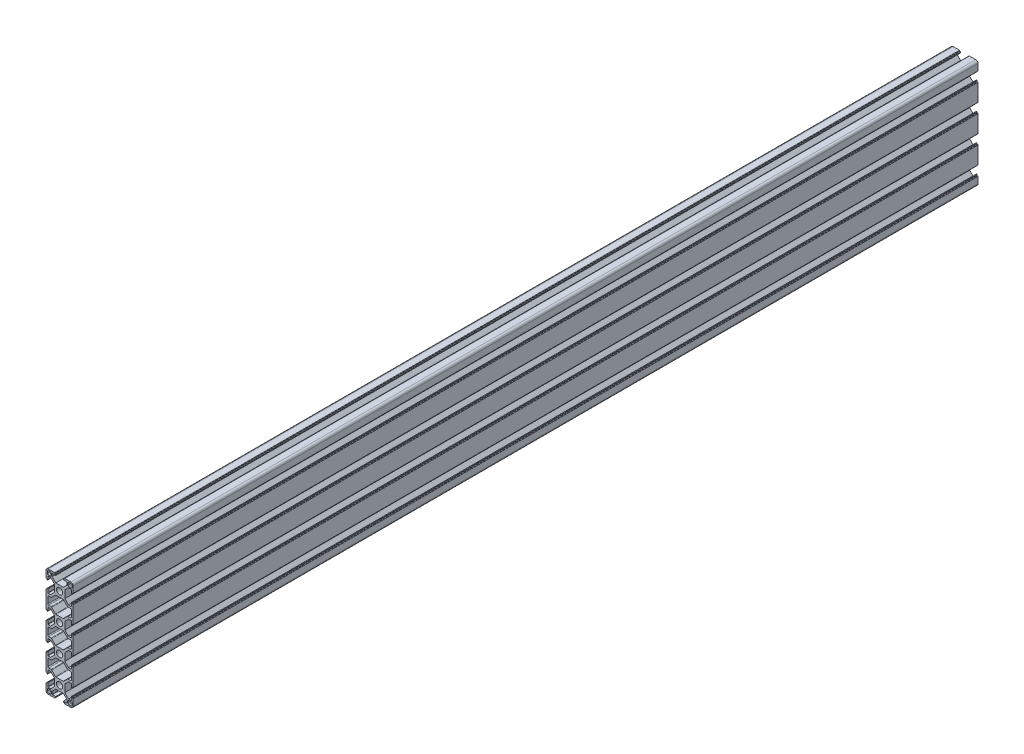
SolidWorks part; units mm, degrees
material "6063 T5"
ref_plane "Спереди" through (0, 0, 0) normal (0, 0, 1) x (1, 0, 0)
ref_plane "Сверху" through (0, 0, 0) normal (0, 1, 0) x (1, 0, 0)
ref_plane "Справа" through (0, 0, 0) normal (1, 0, 0) x (0, 0, -1)
sketch "Эскиз1" plane through (0, 0, 0) normal (0, 0, 1) x (1, 0, 0)
  line L0 (42.4804, 14.8887) -> (42.4804, -45.1113) construction
  line L1 (-15, 8.25) -> (-15, 12.5)
  line L2 (-12.5, 15) -> (-8.25, 15)
  line L3 (8.25, 15) -> (12.5, 15)
  line L4 (15, 12.5) -> (15, 8.25)
  line L5 (12.55, 9.35) -> (10.35, 9.35)
  line L6 (-12.55, 13.55) -> (-10.35, 13.55)
  line L7 (-13.55, 12.55) -> (-13.55, 10.35)
  line L8 (-12.55, 9.35) -> (-10.35, 9.35)
  line L9 (-9.35, 12.55) -> (-9.35, 10.35)
  line L10 (13.55, 12.55) -> (13.55, 10.35)
  line L11 (12.55, 13.55) -> (10.35, 13.55)
  line L12 (9.35, 12.55) -> (9.35, 10.35)
  line L13 (0, 0) -> (0, -30) construction
  line L14 (0, -15) -> (-22.4838, -15) construction
  line L23 (0, -30) -> (0, -60) construction
  line L24 (0, -45) -> (-22.4838, -45) construction
  line L25 (0, -75) -> (-22.4838, -75) construction
  line L26 (0, -90) -> (0, -60) construction
  line L27 (-15, -8.25) -> (-15, -21.75)
  line L28 (15, -8.25) -> (15, -21.75)
  line L29 (-13, -18.5) -> (-13, -11.5)
  line L30 (-12, -10.5) -> (-9.4029, -10.5)
  line L31 (-8.6958, -10.2071) -> (-4.5816, -6.0929)
  line L32 (-3.8745, -5.8) -> (3.8745, -5.8)
  line L33 (8.6958, -10.2071) -> (4.5816, -6.0929)
  line L34 (12, -10.5) -> (9.4029, -10.5)
  line L35 (13, -18.5) -> (13, -11.5)
  line L36 (12, -19.5) -> (9.4029, -19.5)
  line L37 (8.6958, -19.7929) -> (4.5816, -23.9071)
  line L38 (-3.8745, -24.2) -> (3.8745, -24.2)
  line L39 (-8.6958, -19.7929) -> (-4.5816, -23.9071)
  line L40 (-12, -19.5) -> (-9.4029, -19.5)
  line L41 (-12, -70.5) -> (-9.4029, -70.5)
  line L42 (-8.6958, -70.2071) -> (-4.5816, -66.0929)
  line L43 (-3.8745, -65.8) -> (3.8745, -65.8)
  line L44 (8.6958, -70.2071) -> (4.5816, -66.0929)
  line L45 (12, -70.5) -> (9.4029, -70.5)
  line L46 (13, -71.5) -> (13, -78.5)
  line L47 (12, -79.5) -> (9.4029, -79.5)
  line L48 (8.6958, -79.7929) -> (4.5816, -83.9071)
  line L49 (-3.8745, -84.2) -> (3.8745, -84.2)
  line L50 (-8.6958, -79.7929) -> (-4.5816, -83.9071)
  line L51 (-12, -79.5) -> (-9.4029, -79.5)
  line L52 (-13, -71.5) -> (-13, -78.5)
  line L53 (15, -81.75) -> (15, -68.25)
  line L54 (-15, -81.75) -> (-15, -68.25)
  line L55 (9.35, -102.55) -> (9.35, -100.35)
  line L56 (12.55, -103.55) -> (10.35, -103.55)
  line L57 (13.55, -102.55) -> (13.55, -100.35)
  line L58 (-9.35, -102.55) -> (-9.35, -100.35)
  line L59 (-12.55, -99.35) -> (-10.35, -99.35)
  line L60 (-13.55, -102.55) -> (-13.55, -100.35)
  line L61 (-12.55, -103.55) -> (-10.35, -103.55)
  line L62 (12.55, -99.35) -> (10.35, -99.35)
  line L63 (15, -102.5) -> (15, -98.25)
  line L64 (8.25, -105) -> (12.5, -105)
  line L65 (-12.5, -105) -> (-8.25, -105)
  line L66 (-15, -98.25) -> (-15, -102.5)
  line L67 (-15, -38.25) -> (-15, -51.75)
  line L68 (15, -38.25) -> (15, -51.75)
  line L69 (12, -40.5) -> (9.4029, -40.5)
  line L70 (13, -41.5) -> (13, -48.5)
  line L71 (12, -49.5) -> (9.4029, -49.5)
  line L72 (8.6958, -49.7929) -> (4.5816, -53.9071)
  line L73 (-3.8745, -54.2) -> (3.8745, -54.2)
  line L74 (-8.6958, -49.7929) -> (-4.5816, -53.9071)
  line L75 (-12, -49.5) -> (-9.4029, -49.5)
  line L76 (-13, -41.5) -> (-13, -48.5)
  line L77 (-12, -40.5) -> (-9.4029, -40.5)
  line L78 (-8.6958, -40.2071) -> (-4.5816, -36.0929)
  line L79 (-3.8745, -35.8) -> (3.8745, -35.8)
  line L80 (8.6958, -40.2071) -> (4.5816, -36.0929)
  line L81 (-21.0907, 14.8856) -> (-21.0907, -105.1144) construction
  arc A0 (12.5, 15) -> (15, 12.5) centre (12.5, 12.5) cw
  arc A1 (-15, 12.5) -> (-12.5, 15) centre (-12.5, 12.5) cw
  arc A2 (-13.55, 10.35) -> (-12.55, 9.35) centre (-12.55, 10.35) ccw
  arc A3 (-10.35, 9.35) -> (-9.35, 10.35) centre (-10.35, 10.35) ccw
  arc A4 (-10.35, 13.55) -> (-9.35, 12.55) centre (-10.35, 12.55) cw
  arc A5 (-12.55, 13.55) -> (-13.55, 12.55) centre (-12.55, 12.55) ccw
  arc A6 (10.35, 9.35) -> (9.35, 10.35) centre (10.35, 10.35) cw
  arc A7 (13.55, 10.35) -> (12.55, 9.35) centre (12.55, 10.35) cw
  arc A8 (12.55, 13.55) -> (13.55, 12.55) centre (12.55, 12.55) cw
  arc A9 (10.35, 13.55) -> (9.35, 12.55) centre (10.35, 12.55) ccw
  circle A10 centre (0, 0) radius 3.4
  circle A11 centre (0, -30) radius 3.4
  arc A20 (-13, -71.5) -> (-12, -70.5) centre (-12, -71.5) cw
  arc A21 (-9.4029, -70.5) -> (-8.6958, -70.2071) centre (-9.4029, -69.5) ccw
  arc A22 (-4.5816, -6.0929) -> (-3.8745, -5.8) centre (-3.8745, -6.8) cw
  arc A23 (-9.4029, -10.5) -> (-8.6958, -10.2071) centre (-9.4029, -9.5) ccw
  arc A24 (-13, -11.5) -> (-12, -10.5) centre (-12, -11.5) cw
  arc A25 (4.5816, -6.0929) -> (3.8745, -5.8) centre (3.8745, -6.8) ccw
  arc A26 (9.4029, -10.5) -> (8.6958, -10.2071) centre (9.4029, -9.5) cw
  arc A27 (13, -11.5) -> (12, -10.5) centre (12, -11.5) ccw
  arc A28 (13, -18.5) -> (12, -19.5) centre (12, -18.5) cw
  arc A29 (9.4029, -19.5) -> (8.6958, -19.7929) centre (9.4029, -20.5) ccw
  arc A30 (4.5816, -23.9071) -> (3.8745, -24.2) centre (3.8745, -23.2) cw
  arc A31 (-4.5816, -23.9071) -> (-3.8745, -24.2) centre (-3.8745, -23.2) ccw
  arc A32 (-9.4029, -19.5) -> (-8.6958, -19.7929) centre (-9.4029, -20.5) cw
  arc A33 (-13, -18.5) -> (-12, -19.5) centre (-12, -18.5) ccw
  arc A34 (-4.5816, -66.0929) -> (-3.8745, -65.8) centre (-3.8745, -66.8) cw
  arc A35 (4.5816, -66.0929) -> (3.8745, -65.8) centre (3.8745, -66.8) ccw
  arc A36 (9.4029, -70.5) -> (8.6958, -70.2071) centre (9.4029, -69.5) cw
  arc A37 (13, -71.5) -> (12, -70.5) centre (12, -71.5) ccw
  arc A38 (13, -78.5) -> (12, -79.5) centre (12, -78.5) cw
  arc A39 (9.4029, -79.5) -> (8.6958, -79.7929) centre (9.4029, -80.5) ccw
  arc A40 (4.5816, -83.9071) -> (3.8745, -84.2) centre (3.8745, -83.2) cw
  arc A41 (-13, -78.5) -> (-12, -79.5) centre (-12, -78.5) ccw
  arc A42 (-9.4029, -79.5) -> (-8.6958, -79.7929) centre (-9.4029, -80.5) cw
  arc A43 (-4.5816, -83.9071) -> (-3.8745, -84.2) centre (-3.8745, -83.2) ccw
  circle A44 centre (0, -60) radius 3.4
  circle A45 centre (0, -90) radius 3.4
  arc A46 (10.35, -103.55) -> (9.35, -102.55) centre (10.35, -102.55) cw
  arc A47 (12.55, -103.55) -> (13.55, -102.55) centre (12.55, -102.55) ccw
  arc A48 (13.55, -100.35) -> (12.55, -99.35) centre (12.55, -100.35) ccw
  arc A49 (10.35, -99.35) -> (9.35, -100.35) centre (10.35, -100.35) ccw
  arc A50 (-12.55, -103.55) -> (-13.55, -102.55) centre (-12.55, -102.55) cw
  arc A51 (-10.35, -103.55) -> (-9.35, -102.55) centre (-10.35, -102.55) ccw
  arc A52 (-10.35, -99.35) -> (-9.35, -100.35) centre (-10.35, -100.35) cw
  arc A53 (-13.55, -100.35) -> (-12.55, -99.35) centre (-12.55, -100.35) cw
  arc A54 (-15, -102.5) -> (-12.5, -105) centre (-12.5, -102.5) ccw
  arc A55 (12.5, -105) -> (15, -102.5) centre (12.5, -102.5) ccw
  arc A56 (9.4029, -40.5) -> (8.6958, -40.2071) centre (9.4029, -39.5) cw
  arc A57 (13, -41.5) -> (12, -40.5) centre (12, -41.5) ccw
  arc A58 (13, -48.5) -> (12, -49.5) centre (12, -48.5) cw
  arc A59 (9.4029, -49.5) -> (8.6958, -49.7929) centre (9.4029, -50.5) ccw
  arc A60 (4.5816, -53.9071) -> (3.8745, -54.2) centre (3.8745, -53.2) cw
  arc A61 (-4.5816, -53.9071) -> (-3.8745, -54.2) centre (-3.8745, -53.2) ccw
  arc A62 (-9.4029, -49.5) -> (-8.6958, -49.7929) centre (-9.4029, -50.5) cw
  arc A63 (-13, -48.5) -> (-12, -49.5) centre (-12, -48.5) ccw
  arc A64 (-13, -41.5) -> (-12, -40.5) centre (-12, -41.5) cw
  arc A65 (-9.4029, -40.5) -> (-8.6958, -40.2071) centre (-9.4029, -39.5) ccw
  arc A66 (-4.5816, -36.0929) -> (-3.8745, -35.8) centre (-3.8745, -36.8) cw
  arc A67 (4.5816, -36.0929) -> (3.8745, -35.8) centre (3.8745, -36.8) ccw
  point P4 (0, 0)
  point P24 (-9.35, 13.55)
  point P27 (-13.55, 13.55)
  point P77 (0, -30)
  point P100 (0, -5.8)
  point P110 (13, -15)
  point P127 (-13, -15)
  point P172 (-13, -75)
  point P173 (13, -75)
  point P174 (0, -84.2)
  point P175 (0, -60)
  point P176 (-13.55, -103.55)
  point P177 (-9.35, -103.55)
  point P178 (0, -90)
  line B0 (-15, 8.25) -> (-15, 5.5)
  line B1 (-14.7, 5.2) -> (-14.3, 5.2)
  line B2 (-14, 4.9) -> (-14, 4.4)
  line B3 (-13.7, 4.1) -> (-13.3, 4.1)
  line B4 (-13, 4.4) -> (-13, 7.95)
  line B5 (-12.7, 8.25) -> (-9.85, 8.25)
  line B6 (-9.85, 8.25) -> (-5.8, 4.2)
  line B7 (-5.8, 0) -> (-15, 0) construction
  line B8 (-5.8, -4.2) -> (-5.8, 4.2)
  line B9 (-9.85, -8.25) -> (-5.8, -4.2)
  line B10 (-12.7, -8.25) -> (-9.85, -8.25)
  line B11 (-13, -4.4) -> (-13, -7.95)
  line B12 (-13.7, -4.1) -> (-13.3, -4.1)
  line B13 (-14, -4.9) -> (-14, -4.4)
  line B14 (-14.7, -5.2) -> (-14.3, -5.2)
  line B15 (-15, -8.25) -> (-15, -5.5)
  arc B16 (-13, 7.95) -> (-12.7, 8.25) centre (-12.7, 7.95) cw
  arc B17 (-13.3, 4.1) -> (-13, 4.4) centre (-13.3, 4.4) ccw
  arc B18 (-14, 4.4) -> (-13.7, 4.1) centre (-13.7, 4.4) ccw
  arc B19 (-14.3, 5.2) -> (-14, 4.9) centre (-14.3, 4.9) cw
  arc B20 (-15, 5.5) -> (-14.7, 5.2) centre (-14.7, 5.5) ccw
  arc B21 (-15, -5.5) -> (-14.7, -5.2) centre (-14.7, -5.5) cw
  arc B22 (-14.3, -5.2) -> (-14, -4.9) centre (-14.3, -4.9) ccw
  arc B23 (-14, -4.4) -> (-13.7, -4.1) centre (-13.7, -4.4) cw
  arc B24 (-13.3, -4.1) -> (-13, -4.4) centre (-13.3, -4.4) cw
  arc B25 (-13, -7.95) -> (-12.7, -8.25) centre (-12.7, -7.95) ccw
  line B26 (8.25, 15) -> (5.5, 15)
  line B27 (5.2, 14.7) -> (5.2, 14.3)
  line B28 (4.9, 14) -> (4.4, 14)
  line B29 (4.1, 13.7) -> (4.1, 13.3)
  line B30 (4.4, 13) -> (7.95, 13)
  line B31 (8.25, 12.7) -> (8.25, 9.85)
  line B32 (8.25, 9.85) -> (4.2, 5.8)
  line B33 (0, 5.8) -> (0, 15) construction
  line B34 (-4.2, 5.8) -> (4.2, 5.8)
  line B35 (-8.25, 9.85) -> (-4.2, 5.8)
  line B36 (-8.25, 12.7) -> (-8.25, 9.85)
  line B37 (-4.4, 13) -> (-7.95, 13)
  line B38 (-4.1, 13.7) -> (-4.1, 13.3)
  line B39 (-4.9, 14) -> (-4.4, 14)
  line B40 (-5.2, 14.7) -> (-5.2, 14.3)
  line B41 (-8.25, 15) -> (-5.5, 15)
  arc B42 (7.95, 13) -> (8.25, 12.7) centre (7.95, 12.7) cw
  arc B43 (4.1, 13.3) -> (4.4, 13) centre (4.4, 13.3) ccw
  arc B44 (4.4, 14) -> (4.1, 13.7) centre (4.4, 13.7) ccw
  arc B45 (5.2, 14.3) -> (4.9, 14) centre (4.9, 14.3) cw
  arc B46 (5.5, 15) -> (5.2, 14.7) centre (5.5, 14.7) ccw
  arc B47 (-5.5, 15) -> (-5.2, 14.7) centre (-5.5, 14.7) cw
  arc B48 (-5.2, 14.3) -> (-4.9, 14) centre (-4.9, 14.3) ccw
  arc B49 (-4.4, 14) -> (-4.1, 13.7) centre (-4.4, 13.7) cw
  arc B50 (-4.1, 13.3) -> (-4.4, 13) centre (-4.4, 13.3) cw
  arc B51 (-7.95, 13) -> (-8.25, 12.7) centre (-7.95, 12.7) ccw
  line B52 (15, -8.25) -> (15, -5.5)
  line B53 (14.7, -5.2) -> (14.3, -5.2)
  line B54 (14, -4.9) -> (14, -4.4)
  line B55 (13.7, -4.1) -> (13.3, -4.1)
  line B56 (13, -4.4) -> (13, -7.95)
  line B57 (12.7, -8.25) -> (9.85, -8.25)
  line B58 (9.85, -8.25) -> (5.8, -4.2)
  line B59 (5.8, 0) -> (15, 0) construction
  line B60 (5.8, 4.2) -> (5.8, -4.2)
  line B61 (9.85, 8.25) -> (5.8, 4.2)
  line B62 (12.7, 8.25) -> (9.85, 8.25)
  line B63 (13, 4.4) -> (13, 7.95)
  line B64 (13.7, 4.1) -> (13.3, 4.1)
  line B65 (14, 4.9) -> (14, 4.4)
  line B66 (14.7, 5.2) -> (14.3, 5.2)
  line B67 (15, 8.25) -> (15, 5.5)
  arc B68 (13, -7.95) -> (12.7, -8.25) centre (12.7, -7.95) cw
  arc B69 (13.3, -4.1) -> (13, -4.4) centre (13.3, -4.4) ccw
  arc B70 (14, -4.4) -> (13.7, -4.1) centre (13.7, -4.4) ccw
  arc B71 (14.3, -5.2) -> (14, -4.9) centre (14.3, -4.9) cw
  arc B72 (15, -5.5) -> (14.7, -5.2) centre (14.7, -5.5) ccw
  arc B73 (15, 5.5) -> (14.7, 5.2) centre (14.7, 5.5) cw
  arc B74 (14.3, 5.2) -> (14, 4.9) centre (14.3, 4.9) ccw
  arc B75 (14, 4.4) -> (13.7, 4.1) centre (13.7, 4.4) cw
  arc B76 (13.3, 4.1) -> (13, 4.4) centre (13.3, 4.4) cw
  arc B77 (13, 7.95) -> (12.7, 8.25) centre (12.7, 7.95) ccw
  line B78 (-15, -38.25) -> (-15, -35.5)
  line B79 (-14.7, -35.2) -> (-14.3, -35.2)
  line B80 (-14, -34.9) -> (-14, -34.4)
  line B81 (-13.7, -34.1) -> (-13.3, -34.1)
  line B82 (-13, -34.4) -> (-13, -37.95)
  line B83 (-12.7, -38.25) -> (-9.85, -38.25)
  line B84 (-9.85, -38.25) -> (-5.8, -34.2)
  line B85 (-5.8, -30) -> (-15, -30) construction
  line B86 (-5.8, -25.8) -> (-5.8, -34.2)
  line B87 (-9.85, -21.75) -> (-5.8, -25.8)
  line B88 (-12.7, -21.75) -> (-9.85, -21.75)
  line B89 (-13, -25.6) -> (-13, -22.05)
  line B90 (-13.7, -25.9) -> (-13.3, -25.9)
  line B91 (-14, -25.1) -> (-14, -25.6)
  line B92 (-14.7, -24.8) -> (-14.3, -24.8)
  line B93 (-15, -21.75) -> (-15, -24.5)
  arc B94 (-13, -37.95) -> (-12.7, -38.25) centre (-12.7, -37.95) ccw
  arc B95 (-13.3, -34.1) -> (-13, -34.4) centre (-13.3, -34.4) cw
  arc B96 (-14, -34.4) -> (-13.7, -34.1) centre (-13.7, -34.4) cw
  arc B97 (-14.3, -35.2) -> (-14, -34.9) centre (-14.3, -34.9) ccw
  arc B98 (-15, -35.5) -> (-14.7, -35.2) centre (-14.7, -35.5) cw
  arc B99 (-15, -24.5) -> (-14.7, -24.8) centre (-14.7, -24.5) ccw
  arc B100 (-14.3, -24.8) -> (-14, -25.1) centre (-14.3, -25.1) cw
  arc B101 (-14, -25.6) -> (-13.7, -25.9) centre (-13.7, -25.6) ccw
  arc B102 (-13.3, -25.9) -> (-13, -25.6) centre (-13.3, -25.6) ccw
  arc B103 (-13, -22.05) -> (-12.7, -21.75) centre (-12.7, -22.05) cw
  line B104 (15, -21.75) -> (15, -24.5)
  line B105 (14.7, -24.8) -> (14.3, -24.8)
  line B106 (14, -25.1) -> (14, -25.6)
  line B107 (13.7, -25.9) -> (13.3, -25.9)
  line B108 (13, -25.6) -> (13, -22.05)
  line B109 (12.7, -21.75) -> (9.85, -21.75)
  line B110 (9.85, -21.75) -> (5.8, -25.8)
  line B111 (5.8, -30) -> (15, -30) construction
  line B112 (5.8, -34.2) -> (5.8, -25.8)
  line B113 (9.85, -38.25) -> (5.8, -34.2)
  line B114 (12.7, -38.25) -> (9.85, -38.25)
  line B115 (13, -34.4) -> (13, -37.95)
  line B116 (13.7, -34.1) -> (13.3, -34.1)
  line B117 (14, -34.9) -> (14, -34.4)
  line B118 (14.7, -35.2) -> (14.3, -35.2)
  line B119 (15, -38.25) -> (15, -35.5)
  arc B120 (13, -22.05) -> (12.7, -21.75) centre (12.7, -22.05) ccw
  arc B121 (13.3, -25.9) -> (13, -25.6) centre (13.3, -25.6) cw
  arc B122 (14, -25.6) -> (13.7, -25.9) centre (13.7, -25.6) cw
  arc B123 (14.3, -24.8) -> (14, -25.1) centre (14.3, -25.1) ccw
  arc B124 (15, -24.5) -> (14.7, -24.8) centre (14.7, -24.5) cw
  arc B125 (15, -35.5) -> (14.7, -35.2) centre (14.7, -35.5) ccw
  arc B126 (14.3, -35.2) -> (14, -34.9) centre (14.3, -34.9) cw
  arc B127 (14, -34.4) -> (13.7, -34.1) centre (13.7, -34.4) ccw
  arc B128 (13.3, -34.1) -> (13, -34.4) centre (13.3, -34.4) ccw
  arc B129 (13, -37.95) -> (12.7, -38.25) centre (12.7, -37.95) cw
  line B130 (15, -81.75) -> (15, -84.5)
  line B131 (14.7, -84.8) -> (14.3, -84.8)
  line B132 (14, -85.1) -> (14, -85.6)
  line B133 (13.7, -85.9) -> (13.3, -85.9)
  line B134 (13, -85.6) -> (13, -82.05)
  line B135 (12.7, -81.75) -> (9.85, -81.75)
  line B136 (9.85, -81.75) -> (5.8, -85.8)
  line B137 (5.8, -90) -> (15, -90) construction
  line B138 (5.8, -94.2) -> (5.8, -85.8)
  line B139 (9.85, -98.25) -> (5.8, -94.2)
  line B140 (12.7, -98.25) -> (9.85, -98.25)
  line B141 (13, -94.4) -> (13, -97.95)
  line B142 (13.7, -94.1) -> (13.3, -94.1)
  line B143 (14, -94.9) -> (14, -94.4)
  line B144 (14.7, -95.2) -> (14.3, -95.2)
  line B145 (15, -98.25) -> (15, -95.5)
  arc B146 (13, -82.05) -> (12.7, -81.75) centre (12.7, -82.05) ccw
  arc B147 (13.3, -85.9) -> (13, -85.6) centre (13.3, -85.6) cw
  arc B148 (14, -85.6) -> (13.7, -85.9) centre (13.7, -85.6) cw
  arc B149 (14.3, -84.8) -> (14, -85.1) centre (14.3, -85.1) ccw
  arc B150 (15, -84.5) -> (14.7, -84.8) centre (14.7, -84.5) cw
  arc B151 (15, -95.5) -> (14.7, -95.2) centre (14.7, -95.5) ccw
  arc B152 (14.3, -95.2) -> (14, -94.9) centre (14.3, -94.9) cw
  arc B153 (14, -94.4) -> (13.7, -94.1) centre (13.7, -94.4) ccw
  arc B154 (13.3, -94.1) -> (13, -94.4) centre (13.3, -94.4) ccw
  arc B155 (13, -97.95) -> (12.7, -98.25) centre (12.7, -97.95) cw
  line B156 (15, -68.25) -> (15, -65.5)
  line B157 (14.7, -65.2) -> (14.3, -65.2)
  line B158 (14, -64.9) -> (14, -64.4)
  line B159 (13.7, -64.1) -> (13.3, -64.1)
  line B160 (13, -64.4) -> (13, -67.95)
  line B161 (12.7, -68.25) -> (9.85, -68.25)
  line B162 (9.85, -68.25) -> (5.8, -64.2)
  line B163 (5.8, -60) -> (15, -60) construction
  line B164 (5.8, -55.8) -> (5.8, -64.2)
  line B165 (9.85, -51.75) -> (5.8, -55.8)
  line B166 (12.7, -51.75) -> (9.85, -51.75)
  line B167 (13, -55.6) -> (13, -52.05)
  line B168 (13.7, -55.9) -> (13.3, -55.9)
  line B169 (14, -55.1) -> (14, -55.6)
  line B170 (14.7, -54.8) -> (14.3, -54.8)
  line B171 (15, -51.75) -> (15, -54.5)
  arc B172 (13, -67.95) -> (12.7, -68.25) centre (12.7, -67.95) cw
  arc B173 (13.3, -64.1) -> (13, -64.4) centre (13.3, -64.4) ccw
  arc B174 (14, -64.4) -> (13.7, -64.1) centre (13.7, -64.4) ccw
  arc B175 (14.3, -65.2) -> (14, -64.9) centre (14.3, -64.9) cw
  arc B176 (15, -65.5) -> (14.7, -65.2) centre (14.7, -65.5) ccw
  arc B177 (15, -54.5) -> (14.7, -54.8) centre (14.7, -54.5) cw
  arc B178 (14.3, -54.8) -> (14, -55.1) centre (14.3, -55.1) ccw
  arc B179 (14, -55.6) -> (13.7, -55.9) centre (13.7, -55.6) cw
  arc B180 (13.3, -55.9) -> (13, -55.6) centre (13.3, -55.6) cw
  arc B181 (13, -52.05) -> (12.7, -51.75) centre (12.7, -52.05) ccw
  line B182 (8.25, -105) -> (5.5, -105)
  line B183 (5.2, -104.7) -> (5.2, -104.3)
  line B184 (4.9, -104) -> (4.4, -104)
  line B185 (4.1, -103.7) -> (4.1, -103.3)
  line B186 (4.4, -103) -> (7.95, -103)
  line B187 (8.25, -102.7) -> (8.25, -99.85)
  line B188 (8.25, -99.85) -> (4.2, -95.8)
  line B189 (0, -95.8) -> (0, -105) construction
  line B190 (-4.2, -95.8) -> (4.2, -95.8)
  line B191 (-8.25, -99.85) -> (-4.2, -95.8)
  line B192 (-8.25, -102.7) -> (-8.25, -99.85)
  line B193 (-4.4, -103) -> (-7.95, -103)
  line B194 (-4.1, -103.7) -> (-4.1, -103.3)
  line B195 (-4.9, -104) -> (-4.4, -104)
  line B196 (-5.2, -104.7) -> (-5.2, -104.3)
  line B197 (-8.25, -105) -> (-5.5, -105)
  arc B198 (7.95, -103) -> (8.25, -102.7) centre (7.95, -102.7) ccw
  arc B199 (4.1, -103.3) -> (4.4, -103) centre (4.4, -103.3) cw
  arc B200 (4.4, -104) -> (4.1, -103.7) centre (4.4, -103.7) cw
  arc B201 (5.2, -104.3) -> (4.9, -104) centre (4.9, -104.3) ccw
  arc B202 (5.5, -105) -> (5.2, -104.7) centre (5.5, -104.7) cw
  arc B203 (-5.5, -105) -> (-5.2, -104.7) centre (-5.5, -104.7) ccw
  arc B204 (-5.2, -104.3) -> (-4.9, -104) centre (-4.9, -104.3) cw
  arc B205 (-4.4, -104) -> (-4.1, -103.7) centre (-4.4, -103.7) ccw
  arc B206 (-4.1, -103.3) -> (-4.4, -103) centre (-4.4, -103.3) ccw
  arc B207 (-7.95, -103) -> (-8.25, -102.7) centre (-7.95, -102.7) cw
  line B208 (-15, -98.25) -> (-15, -95.5)
  line B209 (-14.7, -95.2) -> (-14.3, -95.2)
  line B210 (-14, -94.9) -> (-14, -94.4)
  line B211 (-13.7, -94.1) -> (-13.3, -94.1)
  line B212 (-13, -94.4) -> (-13, -97.95)
  line B213 (-12.7, -98.25) -> (-9.85, -98.25)
  line B214 (-9.85, -98.25) -> (-5.8, -94.2)
  line B215 (-5.8, -90) -> (-15, -90) construction
  line B216 (-5.8, -85.8) -> (-5.8, -94.2)
  line B217 (-9.85, -81.75) -> (-5.8, -85.8)
  line B218 (-12.7, -81.75) -> (-9.85, -81.75)
  line B219 (-13, -85.6) -> (-13, -82.05)
  line B220 (-13.7, -85.9) -> (-13.3, -85.9)
  line B221 (-14, -85.1) -> (-14, -85.6)
  line B222 (-14.7, -84.8) -> (-14.3, -84.8)
  line B223 (-15, -81.75) -> (-15, -84.5)
  arc B224 (-13, -97.95) -> (-12.7, -98.25) centre (-12.7, -97.95) ccw
  arc B225 (-13.3, -94.1) -> (-13, -94.4) centre (-13.3, -94.4) cw
  arc B226 (-14, -94.4) -> (-13.7, -94.1) centre (-13.7, -94.4) cw
  arc B227 (-14.3, -95.2) -> (-14, -94.9) centre (-14.3, -94.9) ccw
  arc B228 (-15, -95.5) -> (-14.7, -95.2) centre (-14.7, -95.5) cw
  arc B229 (-15, -84.5) -> (-14.7, -84.8) centre (-14.7, -84.5) ccw
  arc B230 (-14.3, -84.8) -> (-14, -85.1) centre (-14.3, -85.1) cw
  arc B231 (-14, -85.6) -> (-13.7, -85.9) centre (-13.7, -85.6) ccw
  arc B232 (-13.3, -85.9) -> (-13, -85.6) centre (-13.3, -85.6) ccw
  arc B233 (-13, -82.05) -> (-12.7, -81.75) centre (-12.7, -82.05) cw
  line B234 (-15, -51.75) -> (-15, -54.5)
  line B235 (-14.7, -54.8) -> (-14.3, -54.8)
  line B236 (-14, -55.1) -> (-14, -55.6)
  line B237 (-13.7, -55.9) -> (-13.3, -55.9)
  line B238 (-13, -55.6) -> (-13, -52.05)
  line B239 (-12.7, -51.75) -> (-9.85, -51.75)
  line B240 (-9.85, -51.75) -> (-5.8, -55.8)
  line B241 (-5.8, -60) -> (-15, -60) construction
  line B242 (-5.8, -64.2) -> (-5.8, -55.8)
  line B243 (-9.85, -68.25) -> (-5.8, -64.2)
  line B244 (-12.7, -68.25) -> (-9.85, -68.25)
  line B245 (-13, -64.4) -> (-13, -67.95)
  line B246 (-13.7, -64.1) -> (-13.3, -64.1)
  line B247 (-14, -64.9) -> (-14, -64.4)
  line B248 (-14.7, -65.2) -> (-14.3, -65.2)
  line B249 (-15, -68.25) -> (-15, -65.5)
  arc B250 (-13, -52.05) -> (-12.7, -51.75) centre (-12.7, -52.05) cw
  arc B251 (-13.3, -55.9) -> (-13, -55.6) centre (-13.3, -55.6) ccw
  arc B252 (-14, -55.6) -> (-13.7, -55.9) centre (-13.7, -55.6) ccw
  arc B253 (-14.3, -54.8) -> (-14, -55.1) centre (-14.3, -55.1) cw
  arc B254 (-15, -54.5) -> (-14.7, -54.8) centre (-14.7, -54.5) ccw
  arc B255 (-15, -65.5) -> (-14.7, -65.2) centre (-14.7, -65.5) cw
  arc B256 (-14.3, -65.2) -> (-14, -64.9) centre (-14.3, -64.9) ccw
  arc B257 (-14, -64.4) -> (-13.7, -64.1) centre (-13.7, -64.4) cw
  arc B258 (-13.3, -64.1) -> (-13, -64.4) centre (-13.3, -64.4) cw
  arc B259 (-13, -67.95) -> (-12.7, -68.25) centre (-12.7, -67.95) ccw
  dimension "D8" = 6.8
  dimension "D3" = 2.5
  dimension "D7" = 1
  dimension "D14" = 1
  dimension "D1" = 15
  dimension "D2" = 60
  dimension "D4" = 1.1
  dimension "D5" = 1.1
  dimension "D6" = 4.2
  dimension "D9" = 30
  dimension "D10" = 9
  dimension "D11" = 26
  dimension "D12" = 18.4
  dimension "D13" = 2.2
  dimension "D15" = 120
sketch_block_instance "Блок1-1"
sketch_block "Блок1" parameters "D6"=0.3, "D1"=16.5, "D2"=8.4, "D3"=9.2, "D4"=45, "D5"=10.4, "D7"=2, "D8"=1, "D9"=8.2
sketch_block_instance "Блок1-2"
sketch_block_instance "Блок1-3"
sketch_block_instance "Блок1-5"
sketch_block_instance "Блок1-6"
sketch_block_instance "Блок1-7"
sketch_block_instance "Блок1-8"
sketch_block_instance "Блок1-9"
sketch_block_instance "Блок1-10"
sketch_block_instance "Блок1-11"
extrude "Бобышка-Вытянуть1" add sketch "Эскиз1" along normal blind 1000 contours B115 B129 B114 B113 B112 B110 B109 B120 B108 B121 B107 B122 B106 B123 B105 B124 B104 L28 B52 B72 B53 B71 B54 B70 B55 B69 B56 B68 B57 B58 B60 B61 B62 B77 B63 B76 B64 B75 B65 B74 B66 B73 B67 L4 A0 L3 B26 B46 B27 B45 B28
